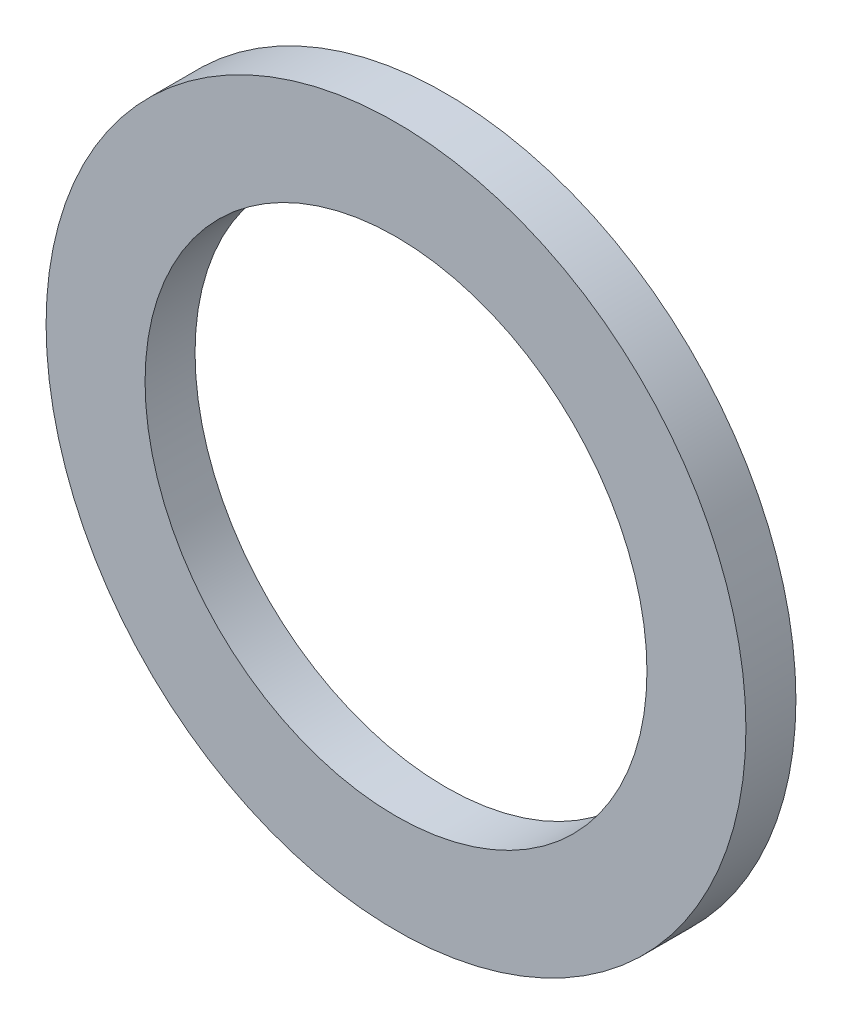
SolidWorks part; units mm, degrees
ref_plane "Front Plane" through (0, 0, 0) normal (0, 0, 1) x (1, 0, 0)
ref_plane "Top Plane" through (0, 0, 0) normal (0, 1, 0) x (1, 0, 0)
ref_plane "Right Plane" through (0, 0, 0) normal (1, 0, 0) x (0, 0, -1)
sketch "Sketch1" plane through (0, 0, 0) normal (0, 0, 1) x (1, 0, 0)
  circle A0 centre (0, 0) radius 15.9385
  circle A1 centre (0, 0) radius 22.225
extrude "Boss-Extrude1" add sketch "Sketch1" along normal blind 3.175
